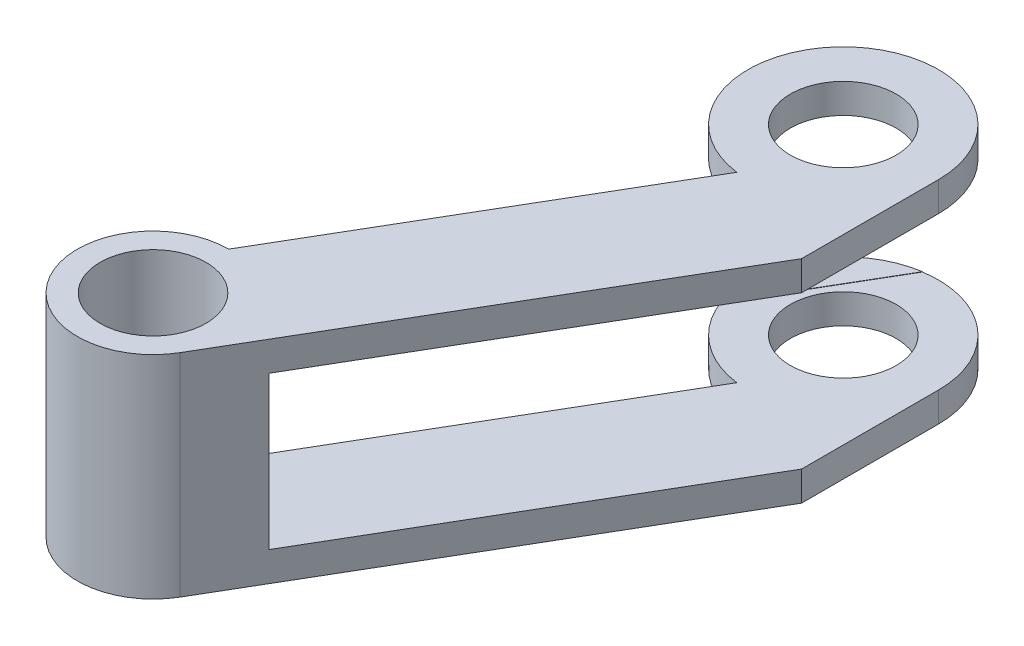
SolidWorks part; units mm, degrees
material "Zirconium"
ref_plane "Front Plane" through (0, 0, 0) normal (0, 0, 1) x (1, 0, 0)
ref_plane "Top Plane" through (0, 0, 0) normal (0, 1, 0) x (1, 0, 0)
ref_plane "Right Plane" through (0, 0, 0) normal (1, 0, 0) x (0, 0, -1)
sketch "Sketch1" plane through (0, 0, 0) normal (0, 1, 0) x (1, 0, 0)
  line L0 (4.5, 0) -> (4.5, -6.4687)
  line L2 (4.5, -6.4687) -> (-6.3309, -24.9868)
  line L3 (-9.417, -19.6067) -> (-0.5608, -4.4649)
  arc A0 (4.5, 0) -> (-0.5608, -4.4649) centre (0, 0) ccw
  arc A1 (-9.417, -19.6067) -> (-6.3309, -24.9868) centre (-9.417, -23.1818) ccw
  dimension "D1" = 9
extrude "Boss-Extrude1" add sketch "Sketch1" along normal blind 10
sketch "Sketch2" plane through (0, 0, 0) normal (0, 0, 1) x (1, 0, 0)
  line L0 (4.5, 10) -> (4.5, 0) construction
  line L1 (13.5, 8.59) -> (-4.5, 8.59)
  line L2 (13.5, 8.59) -> (13.5, 1.41)
  line L3 (13.5, 1.41) -> (-4.5, 1.41)
  line L4 (-4.5, 8.59) -> (-4.5, 1.41)
  line L5 (13.5, 8.59) -> (-4.5, 1.41) construction
  line L6 (13.5, 1.41) -> (-4.5, 8.59) construction
  line L7 (-4.5, 10) -> (-4.5, 0) construction
  point P0 (4.5, 5)
  dimension "D1" = 7.18
extrude "Cut-Extrude1" cut sketch "Sketch2" against normal blind 10 and the other way blind 4.5
sketch "Sketch3" plane through (0, 10, 0) normal (0, 1, 0) x (1, 0, 0)
  circle A0 centre (0, 0) radius 2.5
  dimension "D1" = 5
extrude "Cut-Extrude2" cut sketch "Sketch3" against normal through all
sketch "Sketch4" plane through (0, 10, 0) normal (0, 1, 0) x (1, 0, 0)
  circle A0 centre (-9.417, -23.1818) radius 2.5
  dimension "D1" = 5
extrude "Cut-Extrude3" cut sketch "Sketch4" against normal through all
sketch "Sketch5" plane through (6.1721, 0, 3.6099) normal (0.8632, 0, 0.5049) x (0.5049, 0, -0.8632)
  line L0 (-1.6125, 8.59) -> (-1.6125, 1.41) construction
  line L1 (18.4796, 1.3949) -> (-21.7045, 1.3949)
  line L2 (18.4796, 1.3949) -> (18.4796, 8.6051)
  line L3 (18.4796, 8.6051) -> (-21.7045, 8.6051)
  line L4 (-21.7045, 1.3949) -> (-21.7045, 8.6051)
  line L5 (18.4796, 1.3949) -> (-21.7045, 8.6051) construction
  line L6 (18.4796, 8.6051) -> (-21.7045, 1.3949) construction
  point P0 (-1.6125, 5)
extrude "Cut-Extrude4" cut sketch "Sketch5" against normal blind 10
